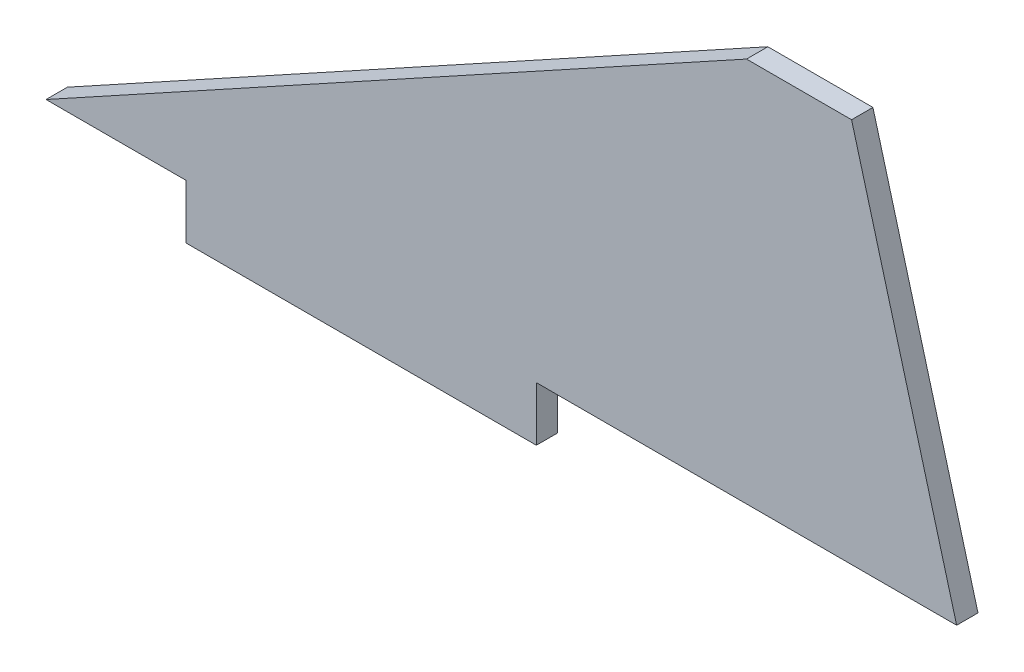
SolidWorks part; units mm, degrees
material "A-Glass Fiber"
ref_plane "Front Plane" through (0, 0, 0) normal (0, 0, 1) x (1, 0, 0)
ref_plane "Top Plane" through (0, 0, 0) normal (0, 1, 0) x (1, 0, 0)
ref_plane "Right Plane" through (0, 0, 0) normal (1, 0, 0) x (0, 0, -1)
sketch "Sketch1" plane through (0, 0, 0) normal (0, 0, 1) x (1, 0, 0)
  line L0 (0, 0) -> (20, 0)
  line L1 (20, 0) -> (20, -7.747)
  line L2 (20, -7.747) -> (70, -7.747)
  line L3 (70, -7.747) -> (70, 0)
  line L4 (70, 0) -> (130, 0)
  line L5 (130, 0) -> (115, 55)
  line L6 (115, 55) -> (100, 55)
  line L7 (100, 55) -> (0, 0)
  dimension "D1" = 20
  dimension "D2" = 7.747
  dimension "D3" = 50
  dimension "D4" = 60
  dimension "D5" = 15
  dimension "D6" = 15
  dimension "D7" = 55
extrude "Boss-Extrude1" add sketch "Sketch1" along normal blind 3.048
